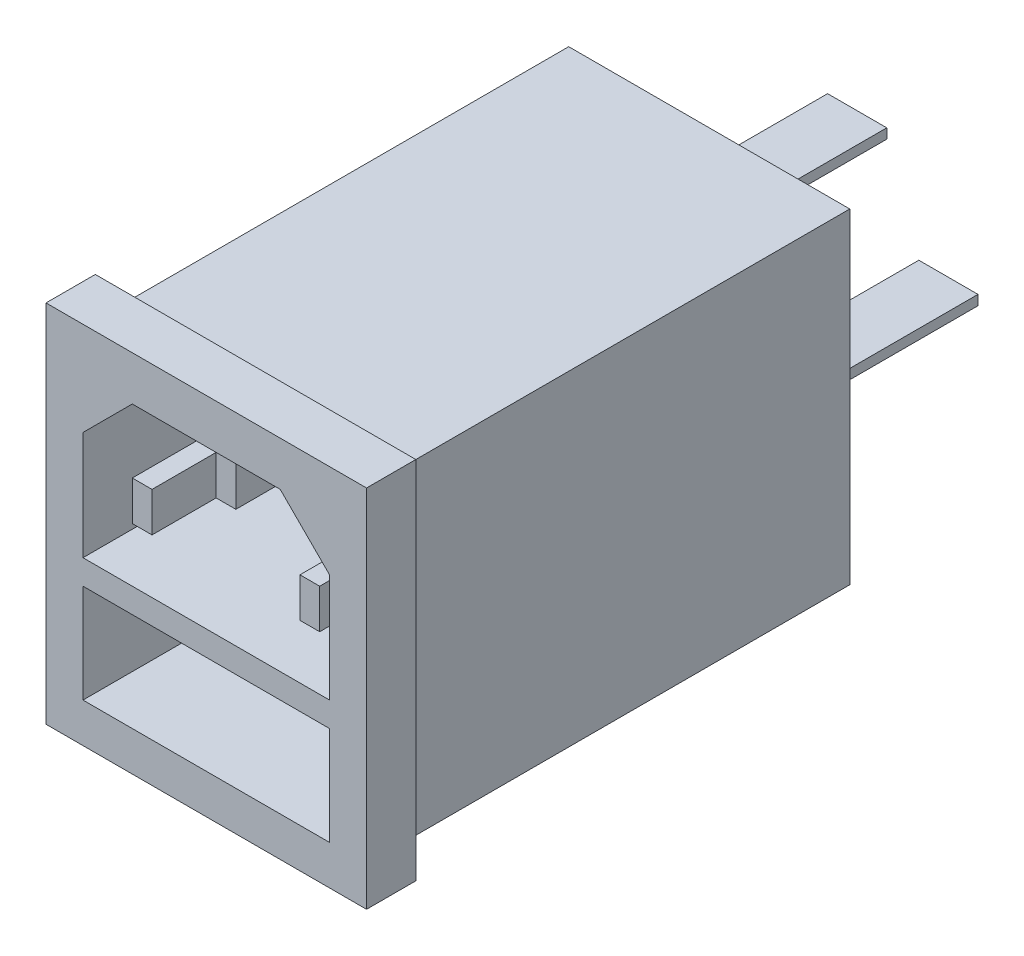
SolidWorks part; units mm, degrees
ref_plane "Front Plane" through (0, 0, 0) normal (0, 0, 1) x (1, 0, 0)
ref_plane "Top Plane" through (0, 0, 0) normal (0, 1, 0) x (1, 0, 0)
ref_plane "Right Plane" through (0, 0, 0) normal (1, 0, 0) x (0, 0, -1)
sketch "Sketch1" plane through (0, 0, 0) normal (0, 0, 1) x (1, 0, 0)
  line L1 (-14.25, -16.5) -> (14.25, -16.5)
  line L2 (-14.25, -16.5) -> (-14.25, 16.5)
  line L3 (-14.25, 16.5) -> (14.25, 16.5)
  line L4 (14.25, -16.5) -> (14.25, 16.5)
  line L5 (-14.25, -16.5) -> (14.25, 16.5) construction
  line L6 (-14.25, 16.5) -> (14.25, -16.5) construction
  point P0 (0, 0)
  dimension "D1" = 33
  dimension "D2" = 28.5
extrude "Boss-Extrude1" add sketch "Sketch1" along normal blind 46
sketch "Sketch2" plane through (0, 0, 46) normal (0, 0, 1) x (1, 0, 0)
  line L0 (14.25, 16.5) -> (-14.25, 16.5) construction
  line L1 (-16.25, -18.5) -> (16.25, -18.5)
  line L2 (-16.25, -18.5) -> (-16.25, 18.5)
  line L3 (-16.25, 18.5) -> (16.25, 18.5)
  line L4 (16.25, -18.5) -> (16.25, 18.5)
  line L5 (-16.25, -18.5) -> (16.25, 18.5) construction
  line L6 (-16.25, 18.5) -> (16.25, -18.5) construction
  line L7 (14.25, -16.5) -> (14.25, 16.5) construction
  point P0 (0, 0)
  point P8 (0, 16.5)
  dimension "D1" = 2
  dimension "D2" = 2
extrude "Boss-Extrude2" add sketch "Sketch2" along normal blind 5
sketch "Sketch3" plane through (0, 0, 51) normal (0, 0, 1) x (1, 0, 0)
  line L0 (0, 13.9521) -> (0, -12.2991) construction
  line L1 (12.5, -2) -> (-12.5, -2)
  line L2 (-12.5, -2) -> (-12.5, 9)
  line L3 (-12.5, 9) -> (-7.5, 14)
  line L4 (-7.5, 14) -> (7.5, 14)
  line L5 (-12.5, -4.5) -> (12.5, -4.5)
  line L6 (-12.5, -4.5) -> (-12.5, -14.5)
  line L7 (-12.5, -14.5) -> (12.5, -14.5)
  line L8 (-16.25, -18.5) -> (16.25, -18.5) construction
  line L9 (12.5, -4.5) -> (12.5, -14.5)
  line L10 (12.5, -2) -> (12.5, 9)
  line L11 (12.5, 9) -> (7.5, 14)
  point P15 (0, -14.5)
  point P16 (0, -4.5)
  point P17 (0, -2)
  point P19 (0, 14)
  dimension "D1" = 12.5
  dimension "D2" = 12.5
  dimension "D3" = 16
  dimension "D4" = 11
  dimension "D5" = 7.5
  dimension "D6" = 10
  dimension "D7" = 4
  dimension "D8" = 2.5
extrude "Cut-Extrude1" cut sketch "Sketch3" against normal blind 17
sketch "Sketch4" plane through (0, 0, 34) normal (0, 0, 1) x (1, 0, 0)
  line L0 (0, 14) -> (0, -2) construction
  line L1 (7.5, 14) -> (-7.5, 14) construction
  line L2 (-12.5, -2) -> (12.5, -2) construction
  line L3 (-12.5, -2) -> (12.5, -2) construction
  line L4 (-9.5, 5.5) -> (-7.5, 5.5)
  line L5 (-9.5, 5.5) -> (-9.5, 1.5)
  line L6 (-9.5, 1.5) -> (-7.5, 1.5)
  line L7 (-7.5, 5.5) -> (-7.5, 1.5)
  line L8 (-9.5, 5.5) -> (-7.5, 1.5) construction
  line L9 (-9.5, 1.5) -> (-7.5, 5.5) construction
  line L10 (-12.5, 9) -> (-12.5, -2) construction
  line L11 (1, 12) -> (-1, 12)
  line L12 (-1, 12) -> (-1, 8)
  line L13 (-1, 8) -> (1, 8)
  line L14 (7.5, 14) -> (-7.5, 14) construction
  line L15 (9.5, 1.5) -> (7.5, 1.5)
  line L16 (9.5, 5.5) -> (9.5, 1.5)
  line L17 (9.5, 5.5) -> (7.5, 5.5)
  line L18 (7.5, 5.5) -> (7.5, 1.5)
  line L19 (1, 12) -> (1, 8)
  point P6 (-8.5, 3.5)
  point P11 (-8.5, 1.5)
  point P20 (-1, 10)
  point P28 (0, 8)
  point P29 (0, 12)
  dimension "D1" = 4
  dimension "D2" = 2
  dimension "D3" = 5.5
  dimension "D4" = 4
  dimension "D5" = 4
  dimension "D6" = 1
  dimension "D7" = 4
extrude "Boss-Extrude3" add sketch "Sketch4" along normal blind 15
sketch "Sketch5" plane through (0, 0, 0) normal (0, 0, -1) x (-1, 0, 0)
  line L0 (0, 11.7617) -> (0, -8.5356) construction
  line L1 (-12.25, 0.5) -> (-6.25, 0.5)
  line L2 (-12.25, 0.5) -> (-12.25, -0.5)
  line L3 (-12.25, -0.5) -> (-6.25, -0.5)
  line L4 (-6.25, 0.5) -> (-6.25, -0.5)
  line L5 (-12.25, 0.5) -> (-6.25, -0.5) construction
  line L6 (-12.25, -0.5) -> (-6.25, 0.5) construction
  line L7 (6.9898, 0) -> (-2.9572, 0) construction
  line L8 (-16.25, -18.5) -> (-16.25, 18.5) construction
  line L9 (3, 10.5) -> (-3, 10.5)
  line L10 (-3, 10.5) -> (-3, 9.5)
  line L11 (-3, 9.5) -> (3, 9.5)
  line L12 (-14.25, 16.5) -> (14.25, 16.5) construction
  line L13 (12.25, 0.5) -> (12.25, -0.5)
  line L14 (12.25, -0.5) -> (6.25, -0.5)
  line L15 (6.25, 0.5) -> (6.25, -0.5)
  line L16 (12.25, 0.5) -> (6.25, 0.5)
  line L17 (3, 10.5) -> (3, 9.5)
  point P0 (-9.25, 0)
  point P23 (0, 9.5)
  point P24 (0, 10.5)
  dimension "D1" = 1
  dimension "D2" = 6
  dimension "D3" = 7
  dimension "D4" = 3
  dimension "D5" = 1
  dimension "D6" = 6
extrude "Boss-Extrude4" add sketch "Sketch5" along normal blind 15
